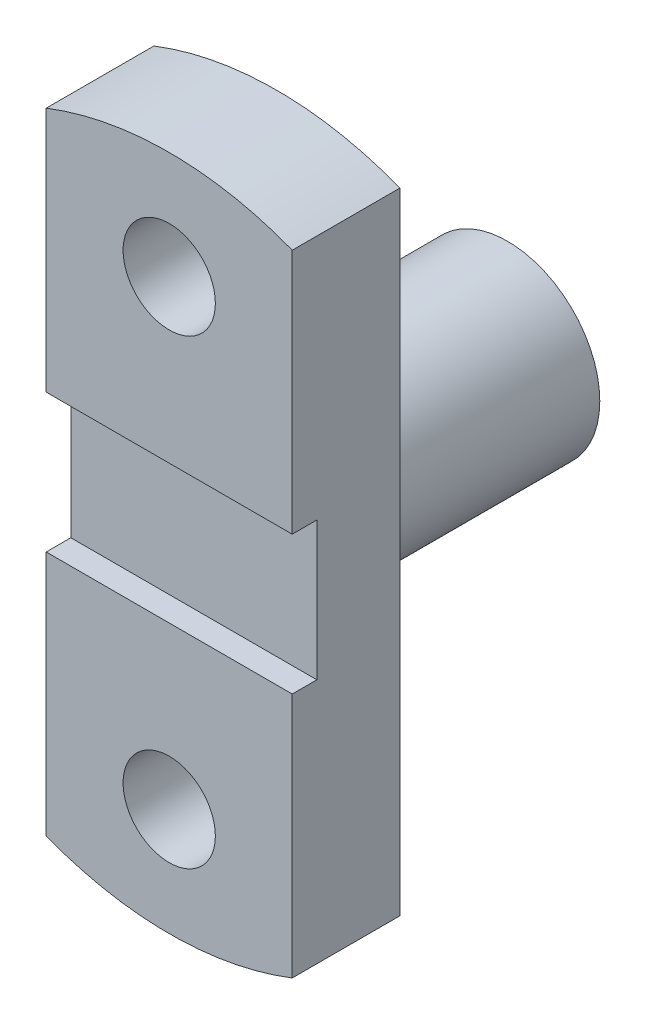
SolidWorks part; units mm, degrees
ref_plane "Front Plane" through (0, 0, 0) normal (0, 0, 1) x (1, 0, 0)
ref_plane "Top Plane" through (0, 0, 0) normal (0, 1, 0) x (1, 0, 0)
ref_plane "Right Plane" through (0, 0, 0) normal (1, 0, 0) x (0, 0, -1)
sketch "Sketch1" plane through (0, 0, 0) normal (0, 0, 1) x (1, 0, 0)
  circle A0 centre (0, 0) radius 30
  dimension "D1" = 60
extrude "Boss-Extrude1" add sketch "Sketch1" along normal blind 75
sketch "Sketch2" plane through (0, 0, 75) normal (0, 0, 1) x (1, 0, 0)
  line L0 (0, -51.5321) -> (0, 63.141) construction
  line L1 (-67.3874, 0) -> (67.4038, 0) construction
  line L2 (-40, 102.4695) -> (-40, -102.4695)
  line L3 (40, -102.4695) -> (40, 102.4695)
  arc A0 (40, 102.4695) -> (-40, 102.4695) centre (0, 0) ccw
  circle A1 centre (0, -75) radius 15
  circle A2 centre (0, 75) radius 15
  arc A3 (-40, -102.4695) -> (40, -102.4695) centre (0, 0) ccw
  point P15 (0, 0)
  point P16 (0, 0)
  dimension "D1" = 220
  dimension "D3" = 150
  dimension "D4" = 30
  dimension "D2" = 80
  dimension "D5" = 75
extrude "Boss-Extrude2" add sketch "Sketch2" along normal blind 35
sketch "Sketch3" plane through (40, 0, 0) normal (1, 0, 0) x (0, 0, -1)
  line L0 (-110, -102.4695) -> (-110, 102.4695) construction
  line L1 (-110, 22.5) -> (-102, 22.5)
  line L2 (-110, 22.5) -> (-110, -22.5)
  line L3 (-110, -22.5) -> (-102, -22.5)
  line L4 (-102, 22.5) -> (-102, -22.5)
  point P6 (-110, 0)
  dimension "D1" = 45
  dimension "D2" = 8
extrude "Cut-Extrude1" cut sketch "Sketch3" against normal up to next
